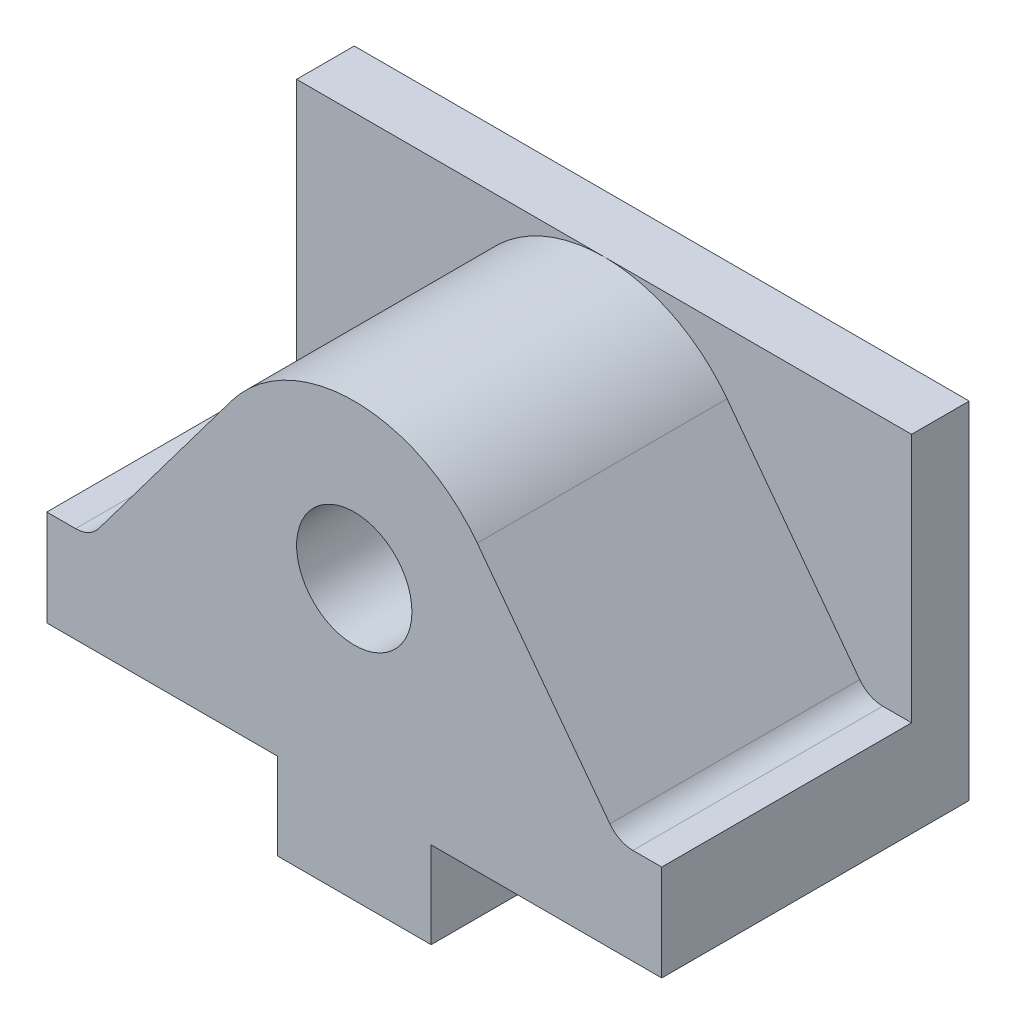
SolidWorks part; units mm, degrees
ref_plane "Front Plane" through (0, 0, 0) normal (0, 0, 1) x (1, 0, 0)
ref_plane "Top Plane" through (0, 0, 0) normal (0, 1, 0) x (1, 0, 0)
ref_plane "Right Plane" through (0, 0, 0) normal (1, 0, 0) x (0, 0, -1)
sketch "Sketch1" plane through (0, 0, 0) normal (0, 1, 0) x (1, 0, 0)
  line L1 (-32, 16) -> (32, 16)
  line L2 (-32, 16) -> (-32, -16)
  line L3 (-32, -16) -> (32, -16)
  line L4 (32, 16) -> (32, -16)
  line L5 (-32, 16) -> (32, -16) construction
  line L6 (-32, -16) -> (32, 16) construction
  point P0 (0, 0)
  dimension "D1" = 32
  dimension "D2" = 64
extrude "Boss-Extrude1" add sketch "Sketch1" along normal blind 36
sketch "Sketch3" plane through (0, 0, 16) normal (0, 0, 1) x (1, 0, 0)
  line L0 (-32, 10) -> (32, 10) construction
  line L1 (-32, 36) -> (-32, 0) construction
  line L2 (32, 36) -> (32, 0) construction
  line L3 (-32, 0) -> (32, 0) construction
  line L4 (-32, 10) -> (-29, 10)
  line L5 (-32, 36) -> (32, 36) construction
  line L6 (32, 10) -> (29, 10)
  line L7 (-26.6, 11.2) -> (-12.8, 29.6)
  line L8 (26.6, 11.2) -> (12.8, 29.6)
  arc A0 (12.8, 29.6) -> (-12.8, 29.6) centre (0, 20) ccw
  arc A1 (29, 10) -> (26.6, 11.2) centre (29, 13) cw
  arc A2 (-29, 10) -> (-26.6, 11.2) centre (-29, 13) ccw
  circle A3 centre (0, 20) radius 6
  point P18 (27.5, 10)
  point P21 (-27.5, 10)
  line M2 (32, 0) -> (32, 36)
  line M3 (32, 36) -> (-32, 36)
  line M4 (-32, 36) -> (-32, 0)
  dimension "D3" = 32
  dimension "D6" = 3
  dimension "D7" = 12
  dimension "D1" = 10
  dimension "D2" = 4.5
  dimension "D4" = 4.5
  dimension "D5" = 55
extrude "Cut-Extrude1" cut sketch "Sketch3" against normal blind 26 contours L4 A2 L7 A0 M3 M4 | A3 | A1 L6 A0 L8 M2 M3
sketch "Sketch4" plane through (0, 0, -10) normal (0, 0, 1) x (1, 0, 0)
  circle A0 centre (0, 20) radius 6
extrude "Cut-Extrude2" cut sketch "Sketch4" against normal blind 26
sketch "Sketch5" plane through (0, 0, 0) normal (0, -1, 0) x (1, 0, 0)
  line L0 (-32, 16) -> (32, 16) construction
  line L2 (-8, 16) -> (-8, -16)
  line L3 (-8, -16) -> (8, -16)
  line L4 (8, 16) -> (8, -16)
  line L5 (32, -16) -> (-32, -16) construction
  line L6 (-8, 16) -> (8, 16)
  point P8 (0, 16)
  point P9 (0, -16)
  dimension "D1" = 16
extrude "Boss-Extrude3" add sketch "Sketch5" along normal blind 9
